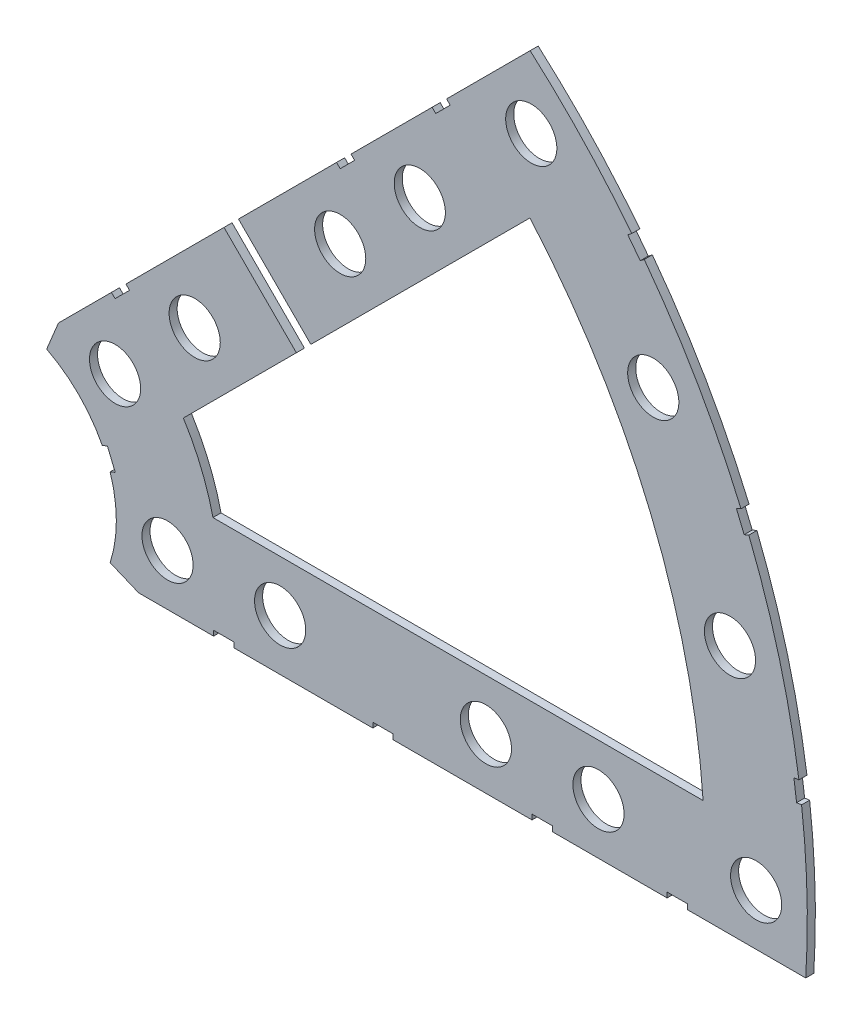
SolidWorks part; units mm, degrees
material "Copper"
ref_plane "Front Plane" through (0, 0, 0) normal (0, 0, 1) x (1, 0, 0)
ref_plane "Top Plane" through (0, 0, 0) normal (0, 1, 0) x (1, 0, 0)
ref_plane "Right Plane" through (0, 0, 0) normal (1, 0, 0) x (0, 0, -1)
sketch "Sketch1" plane through (0, 0, 0) normal (0, 0, 1) x (1, 0, 0)
  line L0 (0, 0) -> (320.3893, 0) construction
  line L1 (0, 0) -> (155.5285, 155.5285) construction
  line L2 (67.2115, 76.1917) -> (8.6967, 17.6769)
  line L3 (8.6967, 17.6769) -> (7.229, 14.1336)
  line L4 (101.4014, -6.35) -> (18.6489, -6.35)
  line L5 (15.1056, -4.8823) -> (18.6489, -6.35)
  line L6 (88.6729, 6.35) -> (27.8605, 6.35)
  line L9 (67.1914, 58.2111) -> (24.1905, 15.2102)
  line L10 (0, 0) -> (40.4486, 97.6516) construction
  line L11 (0, 0) -> (123.4567, -51.1374) construction
  line L18 (8.6967, 17.6769) -> (13.294, 8.6183) construction
  line L19 (18.6489, -6.35) -> (15.4943, 3.3063) construction
  line L20 (27.8605, 6.35) -> (27.7442, 6.7059) construction
  line L21 (24.1905, 15.2102) -> (24.3599, 14.8764) construction
  arc A0 (7.229, 14.1336) -> (15.1056, -4.8823) centre (0, 0) cw
  arc A1 (67.2115, 76.1917) -> (101.4014, -6.35) centre (0, 0) cw
  arc A2 (24.1905, 15.2102) -> (27.8605, 6.35) centre (0, 0) cw
  arc A3 (67.1914, 58.2111) -> (88.6729, 6.35) centre (0, 0) cw
  arc A8 (13.294, 8.6183) -> (15.4943, 3.3063) centre (0, 0) cw construction
  arc A9 (24.3599, 14.8764) -> (27.7442, 6.7059) centre (0, 0) cw construction
  dimension "D1" = 45
  dimension "D3" = 6.35
  dimension "D4" = 15.875
  dimension "D7" = 22.5
  dimension "D8" = 101.6
  dimension "D11" = 12.7
  dimension "D12" = 12.7
  dimension "D2" = 6.35
  dimension "D5" = 67.5
  dimension "D9" = 1.27
  dimension "D10" = 1.27
  dimension "D6" = 12.7
extrude "Boss-Extrude1" add sketch "Sketch1" along normal blind 1
sketch "Sketch2" plane through (0, 0, 1) normal (0, 0, 1) x (1, 0, 0)
  line L0 (0, 0) -> (101.6, 0) construction
  line L1 (0, 0) -> (71.842, 71.842) construction
  line L3 (0, 0) -> (22.225, 0) construction
  line L4 (0, 0) -> (15.7154, 15.7154) construction
  line L5 (0, 0) -> (95.25, 0) construction
  line L6 (0, 0) -> (92.0044, 24.6525) construction
  arc A0 (101.4014, -6.35) -> (67.2115, 76.1917) centre (0, 0) ccw construction
  circle A1 centre (22.225, 0) radius 3.175
  arc A2 (15.1056, -4.8823) -> (7.229, 14.1336) centre (0, 0) ccw construction
  circle A3 centre (36.195, 0) radius 3.175
  circle A4 centre (61.722, 0) radius 3.175
  circle A5 centre (75.692, 0) radius 3.175
  circle A6 centre (95.25, 0) radius 3.175
  circle A7 centre (15.7154, 15.7154) radius 3.175
  circle A8 centre (25.5937, 25.5937) radius 3.175
  circle A9 centre (43.644, 43.644) radius 3.175
  circle A10 centre (53.5223, 53.5223) radius 3.175
  circle A11 centre (92.0044, 24.6525) radius 3.175
  circle A12 centre (82.4889, 47.625) radius 3.175
  circle A13 centre (67.3519, 67.3519) radius 3.175
  dimension "D3" = 6.35
  dimension "D1" = 45
  dimension "D2" = 6.35
  dimension "D4" = 6.35
  dimension "D5" = 13.97
  dimension "D7" = 13.97
  dimension "D8" = 19.558
  dimension "D9" = 45
  dimension "D10" = 15
  dimension "D11" = 25.527
  dimension "D6" = 2
extrude "Cut-Extrude1" cut sketch "Sketch2" against normal through all
sketch "Sketch3" plane through (0, 0, 1) normal (0, 0, 1) x (1, 0, 0)
  line L0 (15.2664, 24.2467) -> (17.0625, 26.0427)
  line L1 (15.2664, 24.2467) -> (15.7154, 23.7977)
  line L2 (17.0625, 26.0427) -> (17.5115, 25.5937)
  line L3 (15.7154, 23.7977) -> (17.5115, 25.5937)
  line L4 (67.2115, 76.1917) -> (8.6967, 17.6769) construction
  line L5 (44.9911, 53.9713) -> (43.195, 52.1753)
  line L6 (44.9911, 53.9713) -> (45.4401, 53.5223)
  line L7 (43.195, 52.1753) -> (43.644, 51.7263)
  line L8 (45.4401, 53.5223) -> (43.644, 51.7263)
  line L9 (27.94, -6.35) -> (30.48, -6.35)
  line L10 (27.94, -6.35) -> (27.94, -5.715)
  line L11 (30.48, -6.35) -> (30.48, -5.715)
  line L12 (27.94, -5.715) -> (30.48, -5.715)
  line L13 (18.6489, -6.35) -> (101.4014, -6.35) construction
  line L14 (67.437, -6.35) -> (69.977, -6.35)
  line L15 (67.437, -6.35) -> (67.437, -5.715)
  line L16 (69.977, -6.35) -> (69.977, -5.715)
  line L17 (67.437, -5.715) -> (69.977, -5.715)
  line L18 (29.2307, 38.211) -> (31.0268, 40.007)
  line L19 (29.2307, 38.211) -> (38.211, 29.2307)
  line L20 (31.0268, 40.007) -> (40.007, 31.0268)
  line L21 (38.211, 29.2307) -> (40.007, 31.0268)
  line L22 (56.845, 65.8253) -> (55.049, 64.0292)
  line L23 (56.845, 65.8253) -> (57.294, 65.3763)
  line L24 (55.049, 64.0292) -> (55.498, 63.5802)
  line L25 (57.294, 65.3763) -> (55.498, 63.5802)
  line L26 (47.6885, -6.35) -> (50.2285, -6.35)
  line L27 (47.6885, -6.35) -> (47.6885, -5.715)
  line L28 (50.2285, -6.35) -> (50.2285, -5.715)
  line L29 (47.6885, -5.715) -> (50.2285, -5.715)
  line L30 (84.201, -6.35) -> (86.741, -6.35)
  line L31 (84.201, -6.35) -> (84.201, -5.715)
  line L32 (86.741, -6.35) -> (86.741, -5.715)
  line L33 (84.201, -5.715) -> (86.741, -5.715)
  line L34 (0, 0) -> (100.7308, 13.2615) construction
  line L35 (0, 0) -> (93.8662, 38.8806) construction
  line L36 (0, 0) -> (80.6047, 61.8502) construction
  line L37 (0, 0) -> (101.6, 0) construction
  line L38 (99.9355, 14.4377) -> (100.267, 11.9194)
  line L39 (99.9355, 14.4377) -> (101.1946, 14.6035)
  line L40 (100.267, 11.9194) -> (101.5261, 12.0852)
  line L41 (101.1946, 14.6035) -> (101.5261, 12.0852)
  line L42 (99.9355, 14.4377) -> (101.5261, 12.0852) construction
  line L43 (100.267, 11.9194) -> (101.1946, 14.6035) construction
  line L44 (93.7655, 37.4643) -> (94.9388, 37.9503)
  line L45 (93.7655, 37.4643) -> (92.7935, 39.811)
  line L46 (94.9388, 37.9503) -> (93.9668, 40.297)
  line L47 (92.7935, 39.811) -> (93.9668, 40.297)
  line L48 (93.7655, 37.4643) -> (93.9668, 40.297) construction
  line L49 (94.9388, 37.9503) -> (92.7935, 39.811) construction
  line L50 (79.3278, 62.4712) -> (80.874, 60.456)
  line L51 (79.3278, 62.4712) -> (80.3354, 63.2443)
  line L52 (80.874, 60.456) -> (81.8816, 61.2292)
  line L53 (80.3354, 63.2443) -> (81.8816, 61.2292)
  line L54 (79.3278, 62.4712) -> (81.8816, 61.2292) construction
  line L55 (80.874, 60.456) -> (80.3354, 63.2443) construction
  line L56 (13.5939, 7.0054) -> (14.5659, 4.6588)
  line L57 (13.5939, 7.0054) -> (14.7672, 7.4914)
  line L58 (14.5659, 4.6588) -> (15.7393, 5.1448)
  line L59 (14.7672, 7.4914) -> (15.7393, 5.1448)
  line L60 (13.5939, 7.0054) -> (15.7393, 5.1448) construction
  line L61 (14.5659, 4.6588) -> (14.7672, 7.4914) construction
  circle A0 centre (15.7154, 15.7154) radius 3.175 construction
  circle A1 centre (43.644, 43.644) radius 3.175 construction
  circle A2 centre (22.225, 0) radius 3.175 construction
  circle A3 centre (61.722, 0) radius 3.175 construction
  arc A4 (101.4014, -6.35) -> (67.2115, 76.1917) centre (0, 0) ccw construction
  circle A6 centre (36.195, 0) radius 3.175 construction
  arc A9 (15.1056, -4.8823) -> (7.229, 14.1336) centre (0, 0) ccw construction
  circle A11 centre (75.692, 0) radius 3.175 construction
  circle A12 centre (25.5937, 25.5937) radius 3.175 construction
  circle A13 centre (53.5223, 53.5223) radius 3.175 construction
  point P75 (14.6666, 6.0751)
  dimension "D2" = 5.715
  dimension "D3" = 2.54
  dimension "D6" = 5.715
  dimension "D8" = 0.635
  dimension "D9" = 5.715
  dimension "D12" = 5.715
  dimension "D4" = 7.5
  dimension "D5" = 22.5
  dimension "D7" = 37.5
  dimension "D10" = 90
  dimension "D11" = 1.27
  dimension "D14" = 0.635
  dimension "D15" = 90
  dimension "D18" = 0.635
  dimension "D19" = 90
  dimension "D22" = 0.635
  dimension "D20" = 1.27
  dimension "D17" = 0.635
  dimension "D21" = 12.7
  dimension "D24" = 2.54
  dimension "D13" = 11.4935
  dimension "D16" = 8.509
  dimension "D23" = 11.4935
  dimension "D25" = 8.509
extrude "Cut-Extrude2" cut sketch "Sketch3" against normal through all
equation "\"cSep\"= 1.005"
equation "\"D11@Sketch2\"=\"cSep\""
equation "\"cSep2\"= \"D8@Sketch2\""
equation "\"D13@Sketch3\"=\"cSep\"/2-.05"
equation "\"D16@Sketch3\"=\"cSep2\"/2-.05"
equation "\"D23@Sketch3\"=\"cSep\"/2-.05"
equation "\"D25@Sketch3\"=\"cSep2\"/2-.05"
